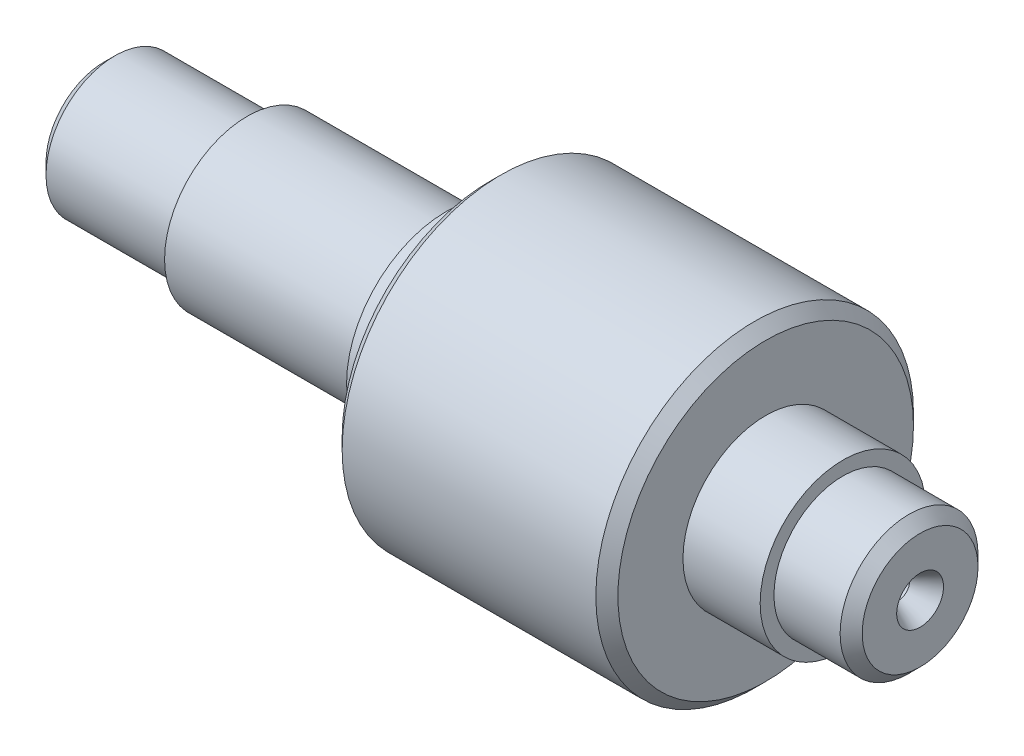
SolidWorks part; units mm, degrees
ref_plane "Спереди" through (0, 0, 0) normal (0, 0, 1) x (1, 0, 0)
ref_plane "Сверху" through (0, 0, 0) normal (0, 1, 0) x (1, 0, 0)
ref_plane "Справа" through (0, 0, 0) normal (1, 0, 0) x (0, 0, -1)
sketch "Эскиз2" plane through (0, 0, 0) normal (0, 0, 1) x (1, 0, 0)
  line L0 (0, 0) -> (148, 0)
  line L1 (148, 0) -> (148, -12.5)
  line L2 (148, -12.5) -> (134, -12.5)
  line L3 (134, -12.5) -> (134, -15)
  line L4 (134, -15) -> (120, -15)
  line L5 (120, -15) -> (120, -28.8)
  line L6 (120, -28.8) -> (70, -28.8)
  line L7 (70, -28.8) -> (70, -18)
  line L8 (70, -18) -> (62, -18)
  line L9 (62, -18) -> (62, -15)
  line L10 (62, -15) -> (26, -15)
  line L11 (26, -15) -> (26, -12.5)
  line L12 (26, -12.5) -> (0, -12.5)
  line L13 (0, -12.5) -> (0, 0)
  point P15 (148, -6.25)
  dimension "D1" = 12.5
  dimension "D2" = 15
  dimension "D3" = 18
  dimension "D4" = 28.8
  dimension "D5" = 15
  dimension "D6" = 12.5
  dimension "D7" = 26
  dimension "D8" = 36
  dimension "D9" = 8
  dimension "D10" = 50
  dimension "D11" = 72
  dimension "D12" = 14
  dimension "D13" = 148
revolve "Повернуть1" add sketch "Эскиз2" angle 360 about L0
sketch "Эскиз3" plane through (0, 0, 0) normal (0, 0, 1) x (1, 0, 0)
  line L0 (0, 0) -> (10.0547, 0)
  line L1 (10.0547, 0) -> (8.9, 2)
  line L2 (8.9, 2) -> (3.9, 2)
  line L3 (3.9, 2) -> (0, 4.25)
  line L4 (0, 12.5) -> (0, -12.5) construction
  line L5 (0, 4.25) -> (0, 0)
  line L6 (0, 0) -> (28.4462, 0) construction
  dimension "D1" = 60
  dimension "D2" = 4
  dimension "D3" = 5
  dimension "D4" = 3.9
  dimension "D5" = 8.5
revolve "Вырез-Повернуть1" cut sketch "Эскиз3" angle 360 about L0
ref_plane "Плоскость4" through (74, 0, 0) normal (1, 0, 0) x (0, 0, -1)
mirror "Зеркальное отражение1" about plane through (74, 0, 0) normal (1, 0, 0) of "Вырез-Повернуть1"
sketch "Эскиз4" plane through (0, 0, 0) normal (0, 0, 1) x (1, 0, 0)
  line L0 (26, 0) -> (62, 0) construction
  line L1 (26, 15) -> (26, -15) construction
  line L2 (62, 18) -> (62, -18) construction
  line L3 (37, 0) -> (51, 0) construction
  line L4 (37, 4) -> (51, 4)
  line L5 (37, -4) -> (51, -4)
  arc A0 (37, 4) -> (37, -4) centre (37, 0) ccw
  arc A1 (51, -4) -> (51, 4) centre (51, 0) ccw
  point P8 (44, 0)
  dimension "D2" = 22
  dimension "D1" = 8
extrude "Вырез-Вытянуть1" cut sketch "Эскиз4" against normal blind 10 from offset 10 offset against normal yes
chamfer "Фаска1" distance 2 angle 45 4 edges at (0, 0, 12.5) (70, 0, 28.8) (120, 0, 28.8) (148, 0, 12.5)
